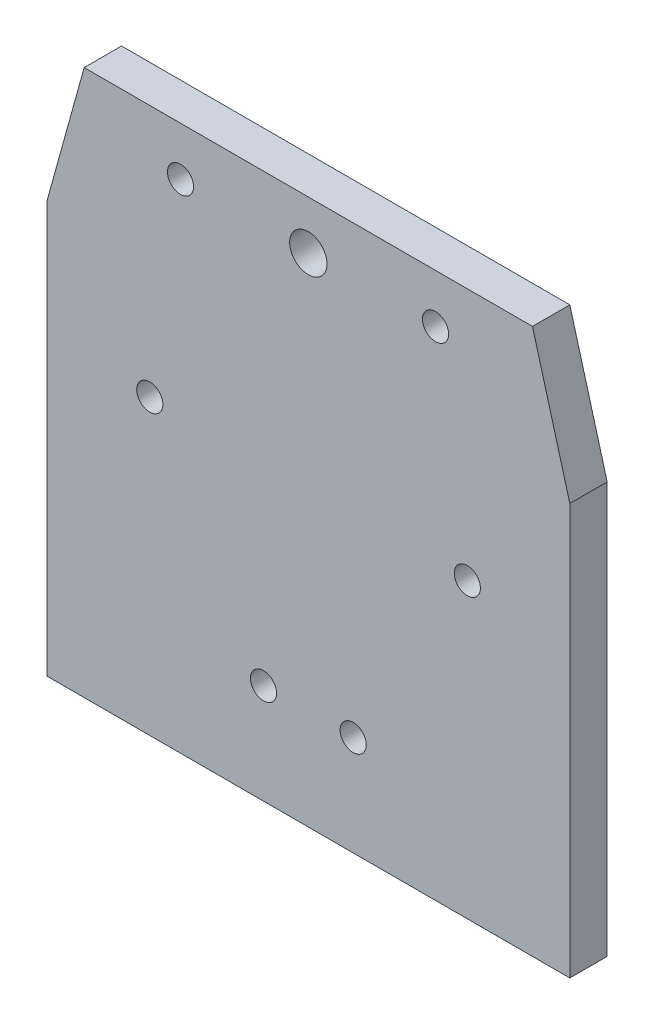
SolidWorks part; units mm, degrees
ref_plane "Front Plane" through (0, 0, 0) normal (0, 0, 1) x (1, 0, 0)
ref_plane "Top Plane" through (0, 0, 0) normal (0, 1, 0) x (1, 0, 0)
ref_plane "Right Plane" through (0, 0, 0) normal (1, 0, 0) x (0, 0, -1)
sketch "Sketch1" plane through (0, 0, 0) normal (0, 0, 1) x (1, 0, 0)
  line L0 (434.9425, 291.2005) -> (434.9425, 236.2005)
  line L1 (434.9425, 236.2005) -> (364.9425, 236.2005)
  line L2 (364.9425, 236.2005) -> (364.9425, 291.2005)
  line L3 (369.9425, 309.2283) -> (429.9425, 309.2283)
  line L4 (364.9425, 291.2005) -> (369.9425, 309.2283)
  line L5 (434.9425, 291.2005) -> (429.9425, 309.2283)
  circle A0 centre (421.2246, 275.3999) radius 1.75
  circle A1 centre (378.7246, 275.4338) radius 1.75
  circle A2 centre (393.9459, 249.5821) radius 1.75
  circle A3 centre (405.9459, 249.5821) radius 1.75
  circle A4 centre (382.8362, 302.7177) radius 1.75
  circle A5 centre (416.9684, 302.7177) radius 1.75
  circle A6 centre (399.9425, 302.7177) radius 2.5
  point P6 (378.7246, 275.4338)
  point P7 (421.2246, 275.3999)
  point P16 (393.9459, 249.5821)
  point P17 (405.9459, 249.5821)
  point P23 (399.9425, 302.7177)
  dimension "D10" = 3.5
  dimension "D4" = 3.5
  dimension "D5" = 3.5
  dimension "D11" = 3.5
  dimension "D12" = 5
  dimension "D1" = 70
  dimension "D2" = 55
  dimension "D3" = 60
  dimension "D6" = 30
  dimension "D8" = 30
  dimension "D7" = 12
  dimension "D9" = 42.5
extrude "Boss-Extrude1" add sketch "Sketch1" along normal blind 5
